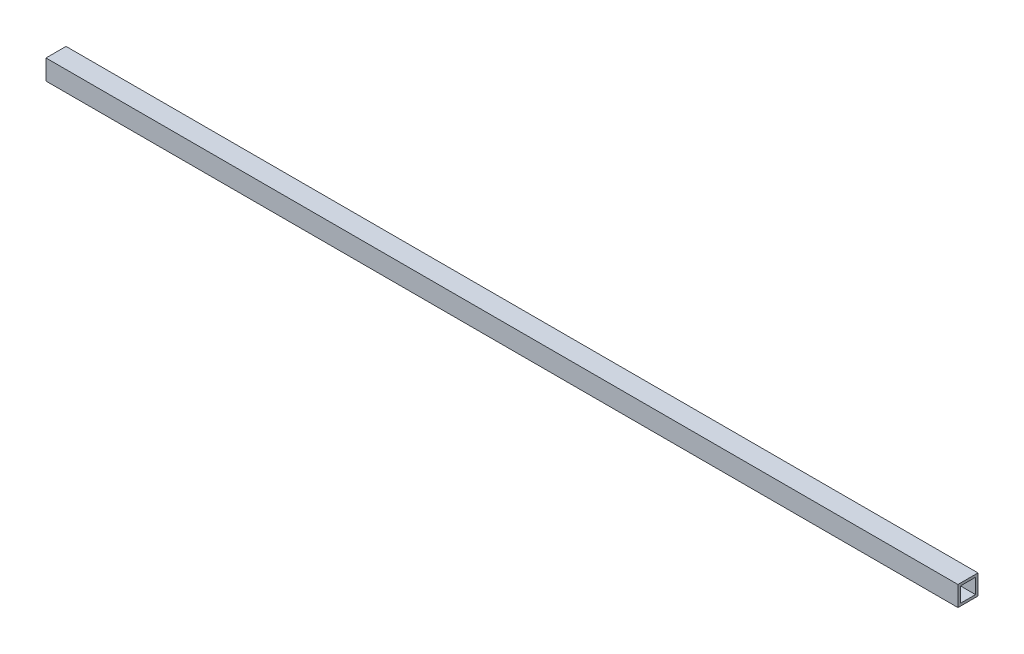
SolidWorks part; units mm, degrees
ref_plane "Piano frontale" through (0, 0, 0) normal (0, 0, 1) x (1, 0, 0)
ref_plane "Piano superiore" through (0, 0, 0) normal (0, 1, 0) x (1, 0, 0)
ref_plane "Piano destro" through (0, 0, 0) normal (1, 0, 0) x (0, 0, -1)
sketch "Schizzo1" plane through (0, 0, 0) normal (1, 0, 0) x (0, -1, 0)
  line L0 (-15, -15) -> (-15, 15)
  line L1 (20, -20) -> (-20, -20)
  line L2 (20, -20) -> (20, 20)
  line L3 (20, 20) -> (-20, 20)
  line L4 (-20, -20) -> (-20, 20)
  line L5 (20, -20) -> (-20, 20) construction
  line L6 (20, 20) -> (-20, -20) construction
  line L7 (15, 15) -> (-15, 15)
  line L8 (15, -15) -> (15, 15)
  line L9 (15, -15) -> (-15, -15)
  point P0 (0, 0)
  dimension "D1" = 40
  dimension "D2" = 40
  dimension "D3" = 5
extrude "Estrusione-Estrusione1" add sketch "Schizzo1" along normal mid plane 1820
